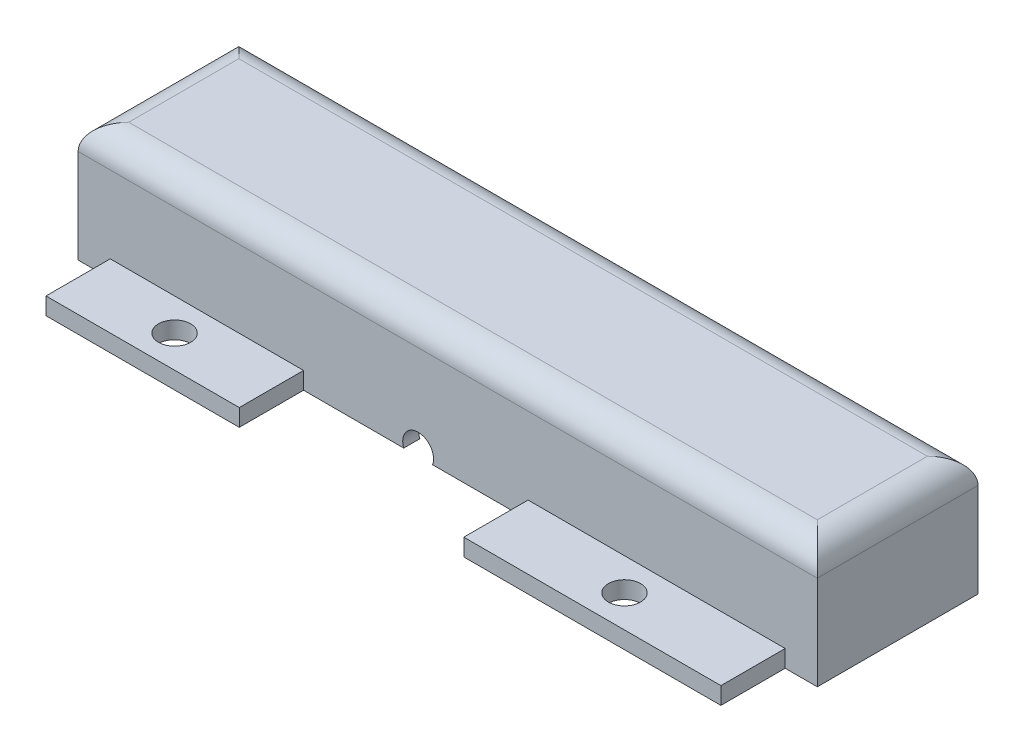
SolidWorks part; units mm, degrees
ref_plane "Front" through (0, 0, 0) normal (0, 0, 1) x (1, 0, 0)
ref_plane "Top" through (0, 0, 0) normal (0, 1, 0) x (1, 0, 0)
ref_plane "Right" through (0, 0, 0) normal (1, 0, 0) x (0, 0, -1)
sketch "Sketch1" plane through (0, 0, 0) normal (0, 0, 1) x (1, 0, 0)
  line L1 (-47.6209, 0) -> (98.4291, 0)
  line L2 (-47.6209, 0) -> (-47.6209, 23.59)
  line L3 (-47.6209, 23.59) -> (98.4291, 23.59)
  line L4 (98.4291, 0) -> (98.4291, 23.59)
  dimension "D1" = 23.59
  dimension "D2" = 146.05
extrude "Boss-Extrude1" add sketch "Sketch1" along normal blind 31.75
sketch "Sketch2" plane through (0, 0, 0) normal (0, -1, 0) x (1, 0, 0)
  line L14 (95.2491, 3.18) -> (95.2491, 28.57)
  line L15 (-44.4409, 3.18) -> (95.2491, 3.18)
  line L16 (-44.4409, 28.57) -> (-44.4409, 3.18)
  line L17 (95.2491, 28.57) -> (-44.4409, 28.57)
  line L18 (95.2491, 3.18) -> (95.2491, 28.57)
  line L19 (-44.4409, 3.18) -> (95.2491, 3.18)
  line L20 (-44.4409, 28.57) -> (-44.4409, 3.18)
  line L21 (95.2491, 28.57) -> (-44.4409, 28.57)
  dimension "D1" = 3.18
extrude "Cut-Extrude1" cut sketch "Sketch2" against normal blind 21
fillet "Fillet1" radius 5 4 edges at (98.4291, 23.59, 15.875) (25.4041, 23.59, 31.75) (-47.6209, 23.59, 15.875) (25.4041, 23.59, 0)
sketch "Sketch3" plane through (0, 0, 31.75) normal (0, 0, 1) x (1, 0, 0)
  line L0 (-47.6209, 18.59) -> (-47.6209, 0) construction
  line L1 (-42.6209, 23.59) -> (93.4291, 23.59) construction
  circle A0 centre (19.5591, 1.09) radius 3.05
  dimension "D1" = 6.1
  dimension "D2" = 67.18
  dimension "D3" = 22.5
extrude "Cut-Extrude2" cut sketch "Sketch3" against normal blind 3.18
sketch "Sketch4" plane through (0, 0, 31.75) normal (0, 0, 1) x (1, 0, 0)
  line L0 (-47.6209, 0) -> (16.7105, 0) construction
  line L1 (-41.2709, 0) -> (-3.0809, 0)
  line L2 (-41.2709, 0) -> (-41.2709, 3.39)
  line L3 (-41.2709, 3.39) -> (-3.0809, 3.39)
  line L4 (-3.0809, 0) -> (-3.0809, 3.39)
  line L5 (22.4076, 0) -> (98.4291, 0) construction
  line L6 (41.2791, 0) -> (92.0791, 0)
  line L7 (41.2791, 0) -> (41.2791, 3.39)
  line L8 (41.2791, 3.39) -> (92.0791, 3.39)
  line L9 (92.0791, 0) -> (92.0791, 3.39)
  line L10 (98.4291, 0) -> (98.4291, 18.59) construction
  dimension "D1" = 38.19
  dimension "D2" = 3.39
  dimension "D3" = 6.35
  dimension "D4" = 50.8
  dimension "D5" = 3.39
  dimension "D6" = 6.35
extrude "Boss-Extrude2" add sketch "Sketch4" along normal blind 12.7
sketch "Sketch5" plane through (0, 0, 0) normal (0, 0, -1) x (-1, 0, 0)
  line L0 (47.6209, 0) -> (-98.4291, 0) construction
  line L1 (-38.4291, 3.39) -> (-13.0291, 3.39)
  line L2 (-38.4291, 3.39) -> (-38.4291, 0)
  line L3 (-38.4291, 0) -> (-13.0291, 0)
  line L4 (-13.0291, 3.39) -> (-13.0291, 0)
  line L5 (-98.4291, 0) -> (-98.4291, 18.59) construction
  dimension "D1" = 25.4
  dimension "D2" = 3.39
  dimension "D3" = 0
  dimension "D4" = 60
extrude "Boss-Extrude3" add sketch "Sketch5" along normal blind 12.7
sketch "Sketch6" plane through (0, 3.39, 0) normal (0, 1, 0) x (1, 0, 0)
  line L0 (92.0791, -44.45) -> (41.2791, -44.45) construction
  line L1 (-3.0809, -44.45) -> (-41.2709, -44.45) construction
  line L2 (41.2791, -44.45) -> (41.2791, -31.75) construction
  line L3 (-41.2709, -44.45) -> (-41.2709, -31.75) construction
  circle A0 centre (-22.2209, -38.1) radius 3.175
  circle A1 centre (66.6791, -38.1) radius 3.175
  dimension "D1" = 6.35
  dimension "D2" = 6.35
  dimension "D3" = 6.35
  dimension "D4" = 6.35
  dimension "D5" = 25.4
  dimension "D6" = 19.05
extrude "Cut-Extrude3" cut sketch "Sketch6" against normal blind 12.7
sketch "Sketch7" plane through (0, 3.39, 0) normal (0, 1, 0) x (1, 0, 0)
  line L0 (13.0291, 12.7) -> (13.0291, 0) construction
  line L1 (13.0291, 12.7) -> (38.4291, 12.7) construction
  circle A0 centre (25.7291, 6.35) radius 3.175
  dimension "D1" = 6.35
  dimension "D2" = 12.7
  dimension "D3" = 6.35
extrude "Cut-Extrude4" cut sketch "Sketch7" against normal blind 12.7
